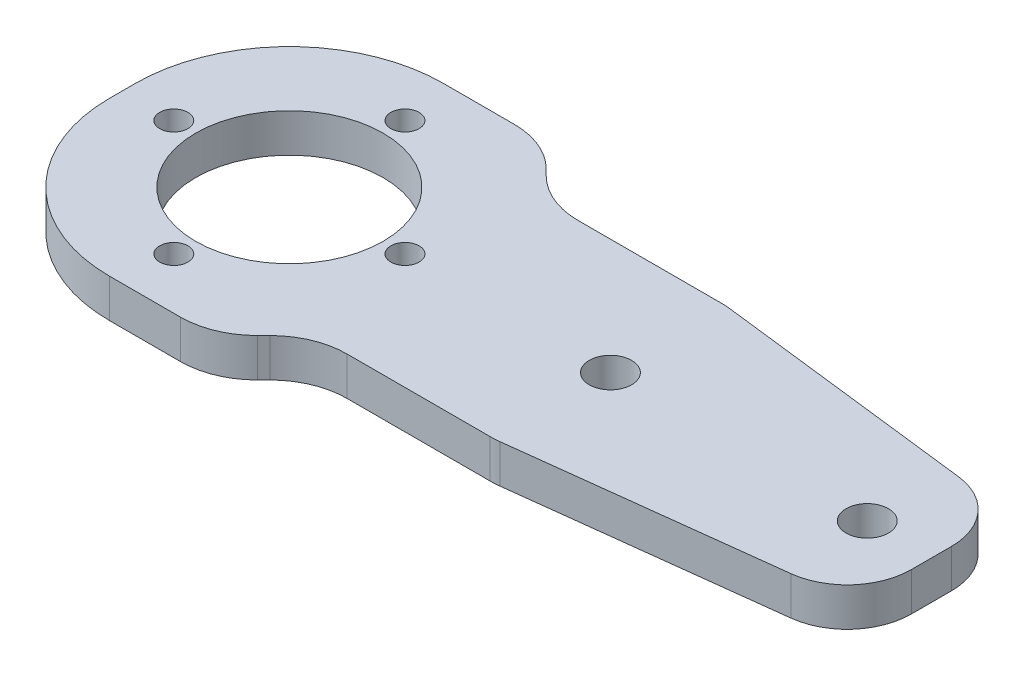
SolidWorks part; units mm, degrees
material "6061-T6 (SS)"
ref_plane "Front Plane" through (0, 0, 0) normal (0, 0, 1) x (1, 0, 0)
ref_plane "Top Plane" through (0, 0, 0) normal (0, 1, 0) x (1, 0, 0)
ref_plane "Right Plane" through (0, 0, 0) normal (1, 0, 0) x (0, 0, -1)
sketch "Sketch1" plane through (0, 0, 0) normal (0, 1, 0) x (1, 0, 0)
  line L0 (20, 26) -> (24, 22)
  line L2 (0, 0) -> (0, 26)
  line L5 (24, 22) -> (38, 22)
  line L6 (38, 22) -> (63, 19)
  line L7 (63, 19) -> (63, 7)
  line L11 (0, 26) -> (20, 26)
  line L12 (0, 0) -> (20, 0)
  line L13 (20, 0) -> (24, 4)
  line L14 (24, 4) -> (38, 4)
  line L15 (38, 4) -> (63, 7)
  circle A0 centre (13, 13) radius 7.3
  circle A2 centre (38, 13) radius 1.65
  circle A3 centre (58, 13) radius 1.65
  dimension "D4" = 14.6
  dimension "D9" = 25
  dimension "D11" = 14
  dimension "D12" = 3.3
  dimension "D13" = 3.3
  dimension "D1" = 26
  dimension "D2" = 4
  dimension "D3" = 13
  dimension "D5" = 4
  dimension "D6" = 4
  dimension "D7" = 20
  dimension "D8" = 0
  dimension "D10" = 14
  dimension "D14" = 6
  dimension "D15" = 13
  dimension "D16" = 0
  dimension "D17" = 6
  dimension "D18" = 5
  dimension "D19" = 5
  dimension "D20" = 20
  dimension "D21" = 20
  dimension "D22" = 4
extrude "Boss-Extrude1" add sketch "Sketch1" along normal blind 3
fillet "Fillet1" radius 12 2 edges at (0, 1.5, -26) (0, 1.5, 0)
fillet "Fillet4" radius 6 6 edges at (38, 1.5, -22) (38, 1.5, -4) (24, 1.5, -4) (24, 1.5, -22) (20, 1.5, -26) (20, 1.5, 0)
fillet "Fillet5" radius 5 2 edges at (63, 1.5, -7) (63, 1.5, -19)
sketch "Sketch2" plane through (0, 3, 0) normal (0, 1, 0) x (1, 0, 0)
  circle A0 centre (22, 13) radius 1.1
  circle A1 centre (13, 13) radius 7.3 construction
  circle A5 centre (13, 4) radius 1.1
  circle A6 centre (4, 13) radius 1.1
  circle A7 centre (13, 22) radius 1.1
  point P13 (13, 13)
  dimension "D2" = 2.2
  dimension "D1" = 9
  dimension "D4" = 0
  dimension "D3" = 4
extrude "Cut-Extrude1" cut sketch "Sketch2" against normal blind 10
